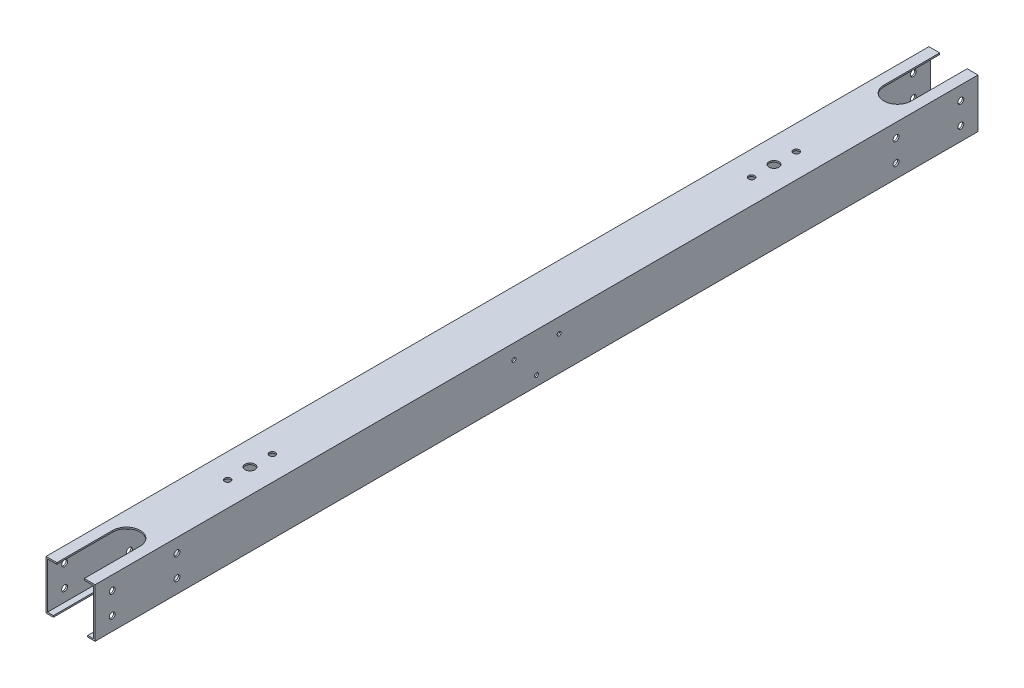
SolidWorks part; units mm, degrees
material "6061 Alloy"
ref_plane "Front Plane" through (0, 0, 0) normal (0, 0, 1) x (1, 0, 0)
ref_plane "Top Plane" through (0, 0, 0) normal (0, 1, 0) x (1, 0, 0)
ref_plane "Right Plane" through (0, 0, 0) normal (1, 0, 0) x (0, 0, -1)
sketch "Sketch1" plane through (0, 0, 0) normal (0, 0, 1) x (1, 0, 0)
  line L1 (-23.5, 23.5) -> (23.5, 23.5)
  line L2 (-23.5, 23.5) -> (-23.5, -23.5)
  line L3 (-23.5, -23.5) -> (23.5, -23.5)
  line L4 (23.5, 23.5) -> (23.5, -23.5)
  line L5 (-23.5, 23.5) -> (23.5, -23.5) construction
  line L6 (-23.5, -23.5) -> (23.5, 23.5) construction
  line L7 (-25, 25) -> (25, 25)
  line L8 (-25, 25) -> (-25, -25)
  line L9 (-25, -25) -> (25, -25)
  line L10 (25, 25) -> (25, -25)
  line L11 (-25, 25) -> (25, -25) construction
  line L12 (-25, -25) -> (25, 25) construction
  point P0 (0, 0)
  point P6 (0, 0)
  dimension "D1" = 50
  dimension "D2" = 47
  dimension "D3" = 50
  dimension "D4" = 47
extrude "Boss-Extrude1" add sketch "Sketch1" along normal blind 900
sketch "Sketch2" plane through (25, 0, 0) normal (1, 0, 0) x (0, 0, -1)
  line L0 (-900, -25) -> (0, -25) construction
  line L1 (-450, -25) -> (-450, 25) construction
  line L2 (-900, 25) -> (0, 25) construction
  line L3 (0, -25) -> (0, 25) construction
  circle A0 centre (-450, -15) radius 2
  circle A1 centre (-427, 10) radius 2
  circle A2 centre (-473, 10) radius 2
  point P0 (-450, -25)
  dimension "D4" = 4
  dimension "D1" = 10
  dimension "D2" = 25
  dimension "D3" = 23
  dimension "D5" = 450
extrude "Cut-Extrude1" cut sketch "Sketch2" against normal blind 59
sketch "Sketch3" plane through (0, 25, 0) normal (0, 1, 0) x (1, 0, 0)
  line L0 (0, -843) -> (0, -913.9861) construction
  line L5 (14, -843) -> (14, -913.9861)
  line L6 (-14, -843) -> (-14, -913.9861)
  line L7 (25, -900) -> (-25, -900) construction
  arc A0 (14, -843) -> (-14, -843) centre (0, -843) ccw
  arc A1 (-14, -913.9861) -> (14, -913.9861) centre (0, -913.9861) ccw
  point P2 (0, -878.4931)
  dimension "D2" = 14
  dimension "D1" = 57
extrude "Cut-Extrude2" cut sketch "Sketch3" against normal blind 10
sketch "Sketch4" plane through (0, -25, 0) normal (0, -1, 0) x (1, 0, 0)
  line L0 (0.0011, 850) -> (0.0011, 939.0785) construction
  line L1 (-17.4989, 850) -> (-17.4989, 939.0785)
  line L2 (17.5011, 850) -> (17.5011, 939.0785)
  line L3 (25, 900) -> (25, 0) construction
  line L4 (-25, 900) -> (25, 900) construction
  arc A0 (-17.4989, 850) -> (17.5011, 850) centre (0.0011, 850) ccw
  arc A1 (17.5011, 939.0785) -> (-17.4989, 939.0785) centre (0.0011, 939.0785) ccw
  point P2 (0.0011, 894.5393)
  dimension "D2" = 17.5
  dimension "D1" = 50
extrude "Cut-Extrude3" cut sketch "Sketch4" against normal blind 10
sketch "Sketch5" plane through (25, 0, 0) normal (1, 0, 0) x (0, 0, -1)
  line L0 (-900, -25) -> (0, -25) construction
  line L1 (-900, 25) -> (0, 25) construction
  line L2 (-900, -25) -> (-900, 25) construction
  line L3 (-849.5, 25) -> (-849.5, -25) construction
  circle A0 centre (-882.5, 11) radius 3
  circle A2 centre (-882.5, -11) radius 3
  circle A3 centre (-816.5, -11) radius 3
  circle A4 centre (-816.5, 11) radius 3
  dimension "D4" = 6
  dimension "D6" = 6
  dimension "D1" = 33
  dimension "D2" = 14
  dimension "D3" = 14
  dimension "D7" = 17.5
extrude "Cut-Extrude4" cut sketch "Sketch5" against normal blind 55
ref_plane "Plane1" through (0, 0, 450) normal (0, 0, 1) x (1, 0, 0)
mirror "Mirror1" about plane through (0, 0, 450) normal (0, 0, 1) of "Cut-Extrude4", "Cut-Extrude3", "Cut-Extrude2"
sketch "Sketch6" plane through (0, 25, 0) normal (0, 1, 0) x (1, 0, 0)
  line L0 (0, -694.2275) -> (0, -739.8525) construction
  line L2 (-27.5, -450) -> (27.5, -450) construction
  circle A0 centre (0, -694.2275) radius 3.125
  circle A1 centre (0, -739.8525) radius 3.125
  circle A2 centre (0, -717.04) radius 5
  point P8 (0, -717.04)
  dimension "D1" = 6.25
  dimension "D2" = 6.25
  dimension "D5" = 10
  dimension "D3" = 45.625
  dimension "D4" = 267.04
extrude "Cut-Extrude5" cut sketch "Sketch6" against normal blind 70
mirror "Mirror2" about plane through (0, 0, 450) normal (0, 0, 1) of "Cut-Extrude5"
